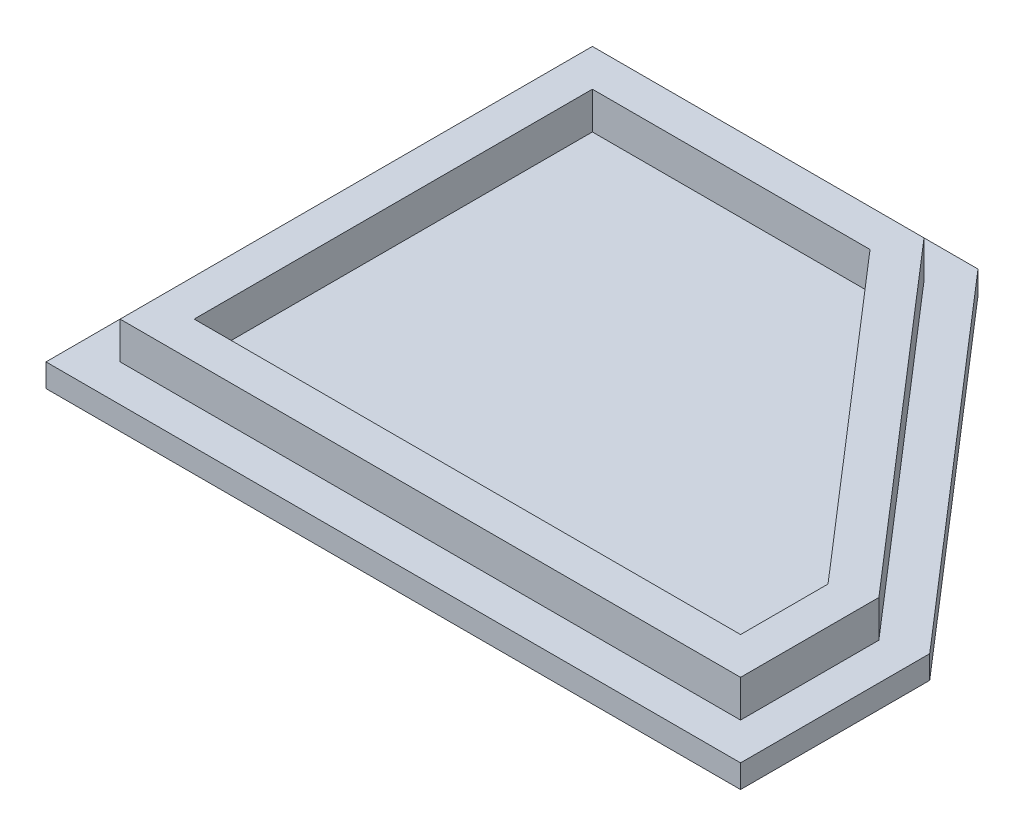
SolidWorks part; units mm, degrees
ref_plane "Front Plane" through (0, 0, 0) normal (0, 0, 1) x (1, 0, 0)
ref_plane "Top Plane" through (0, 0, 0) normal (0, 1, 0) x (1, 0, 0)
ref_plane "Right Plane" through (0, 0, 0) normal (1, 0, 0) x (0, 0, -1)
sketch "Sketch1" plane through (0, 0, 0) normal (0, 1, 0) x (1, 0, 0)
  line L0 (-52.9148, 31.5964) -> (-11.2748, 31.5964)
  line L1 (-11.2748, 31.5964) -> (22.0852, -6.9796)
  line L2 (22.0852, -6.9796) -> (22.0852, -27.4036)
  line L3 (22.0852, -27.4036) -> (-52.9148, -27.4036)
  line L4 (-52.9148, -27.4036) -> (-52.9148, 31.5964)
  point P10 (0, 0)
  dimension "D1" = 41.64
  dimension "D2" = 75
  dimension "D3" = 59
  dimension "D4" = 51
  dimension "D5" = 20.424
extrude "Boss-Extrude2" add sketch "Sketch1" along normal blind 2.5
sketch "Sketch2" plane through (0, 2.5, 0) normal (0, 1, 0) x (1, 0, 0)
  line L0 (-52.9148, 31.5964) -> (-11.2748, 31.5964)
  line L1 (-11.2748, 31.5964) -> (22.0852, -6.9796)
  line L2 (22.0852, -6.9796) -> (22.0852, -27.4036)
  line L3 (22.0852, -27.4036) -> (-52.9148, -27.4036)
  line L4 (-52.9148, -27.4036) -> (-52.9148, 31.5964)
  line L5 (-48.9148, -23.4036) -> (-48.9148, 27.5964)
  line L6 (-48.9148, 27.5964) -> (-13.1039, 27.5964)
  line L7 (-13.1039, 27.5964) -> (18.0852, -8.4693)
  line L8 (18.0852, -8.4693) -> (18.0852, -23.4036)
  line L9 (18.0852, -23.4036) -> (-48.9148, -23.4036)
  line L10 (-44.9148, 23.5964) -> (-14.933, 23.5964)
  line L11 (-14.933, 23.5964) -> (14.0852, -9.959)
  line L12 (14.0852, -9.959) -> (14.0852, -19.4036)
  line L13 (14.0852, -19.4036) -> (-44.9148, -19.4036)
  line L14 (-44.9148, -19.4036) -> (-44.9148, 23.5964)
  dimension "D1" = 4
  dimension "D2" = 4
extrude "Boss-Extrude3" add sketch "Sketch2" along normal blind 4 contours L9 L8 L7 L6 L5 L13 L14 L10 L11 L12
sketch "Sketch3" plane through (0, 2.5, 0) normal (0, 1, 0) x (1, 0, 0)
  line L0 (-48.9148, -16.3456) -> (-44.9148, -16.3456)
  line L1 (-48.9148, -23.4036) -> (-48.9148, 27.5964) construction
  line L3 (-44.9148, -19.4036) -> (-44.9148, 23.5964) construction
  line L4 (-44.9148, -16.3456) -> (-44.9148, -19.4036)
  line L5 (18.0852, -23.4036) -> (-48.9148, -23.4036) construction
  line L6 (-41.5777, -23.4036) -> (-48.9148, -23.4036)
  line L7 (-48.9148, -23.4036) -> (-48.9148, -16.3456)
  line L8 (-44.9148, -19.4036) -> (-41.5777, -19.4036)
  line L9 (14.0852, -19.4036) -> (-44.9148, -19.4036) construction
  line L10 (-41.5777, -19.4036) -> (-41.5777, -23.4036)
  line L11 (14.0852, -16.3456) -> (18.0852, -16.3456)
  line L12 (14.0852, -9.959) -> (14.0852, -19.4036) construction
  line L13 (18.0852, -8.4693) -> (18.0852, -23.4036) construction
  line L14 (18.0852, -16.3456) -> (18.0852, -23.4036)
  line L15 (10.268, -23.4036) -> (10.268, -19.4036)
  line L16 (14.0852, -19.4036) -> (-44.9148, -19.4036) construction
  line L17 (10.268, -19.4036) -> (14.0852, -19.4036)
  line L18 (14.0852, -19.4036) -> (14.0852, -16.3456)
